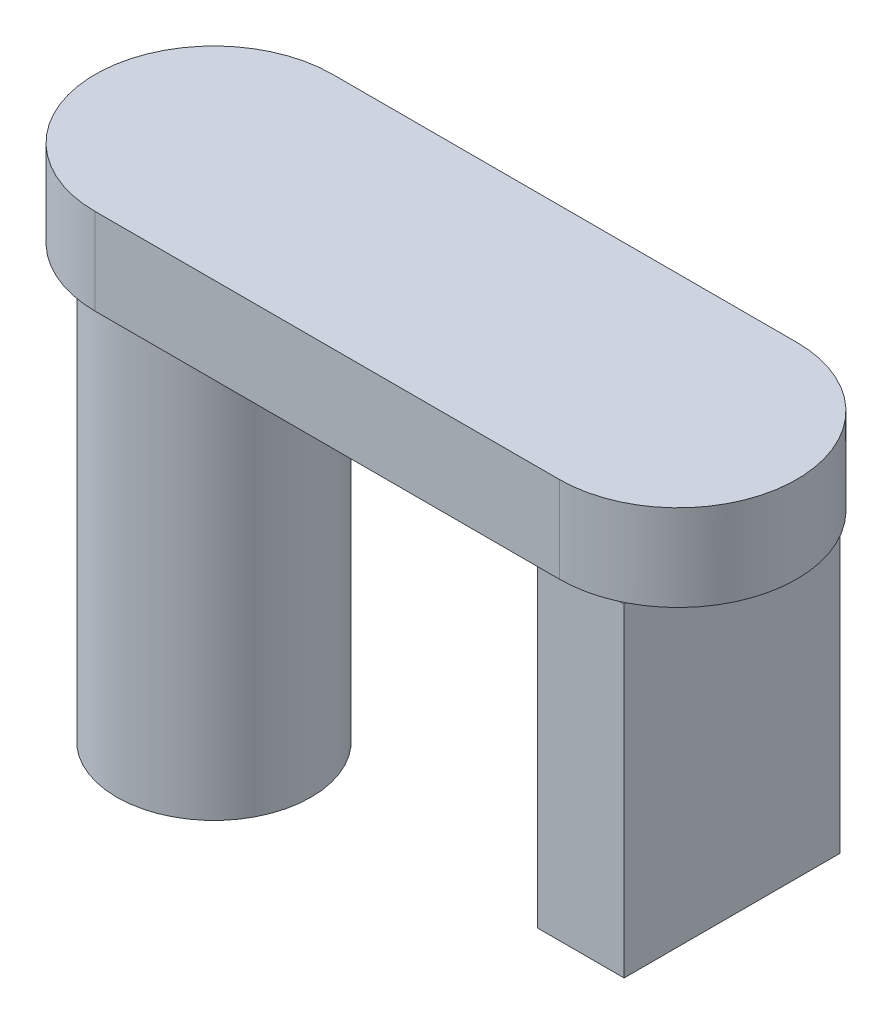
SolidWorks part; units mm, degrees
ref_plane "Front Plane" through (0, 0, 0) normal (0, 0, 1) x (1, 0, 0)
ref_plane "Top Plane" through (0, 0, 0) normal (0, 1, 0) x (1, 0, 0)
ref_plane "Right Plane" through (0, 0, 0) normal (1, 0, 0) x (0, 0, -1)
sketch "Sketch1" plane through (0, 0, 0) normal (0, 1, 0) x (1, 0, 0)
  line L1 (2, 0.5) -> (2.4, 0.5)
  line L2 (2, 0.5) -> (2, -0.5)
  line L3 (2, -0.5) -> (2.4, -0.5)
  line L4 (2.4, 0.5) -> (2.4, -0.5)
  line L5 (2, 0.5) -> (2.4, -0.5) construction
  line L6 (2, -0.5) -> (2.4, 0.5) construction
  circle A0 centre (0, 0) radius 0.45
  point P3 (2.2, 0)
  dimension "D1" = 0.9
  dimension "D2" = 0.4
  dimension "D3" = 1
  dimension "D4" = 0
  dimension "D5" = 2
extrude "Boss-Extrude1" add sketch "Sketch1" along normal blind 2
sketch "Sketch2" plane through (0, 2, 0) normal (0, 1, 0) x (1, 0, 0)
  line L0 (0, 0) -> (2.15, 0) construction
  line L1 (0, 0.55) -> (2.15, 0.55)
  line L2 (0, -0.55) -> (2.15, -0.55)
  line L4 (2.4, -0.5) -> (2.4, 0.5) construction
  arc A0 (0, 0.55) -> (0, -0.55) centre (0, 0) ccw
  arc A1 (2.15, -0.55) -> (2.15, 0.55) centre (2.15, 0) ccw
  circle A2 centre (0, 0) radius 0.45 construction
  point P3 (1.075, 0)
  dimension "D1" = 0.1
  dimension "D2" = 0.25
extrude "Boss-Extrude2" add sketch "Sketch2" along normal blind 0.4
sketch "Sketch3" plane through (0, 0, 0) normal (0, -1, 0) x (1, 0, 0)
  line L1 (2, 0.5) -> (2.4, 0.5)
  line L2 (2, 0.5) -> (2, -0.5)
  line L3 (2, -0.5) -> (2.4, -0.5)
  line L4 (2.4, 0.5) -> (2.4, -0.5)
extrude "Cut-Extrude1" cut sketch "Sketch3" against normal blind 0.5
